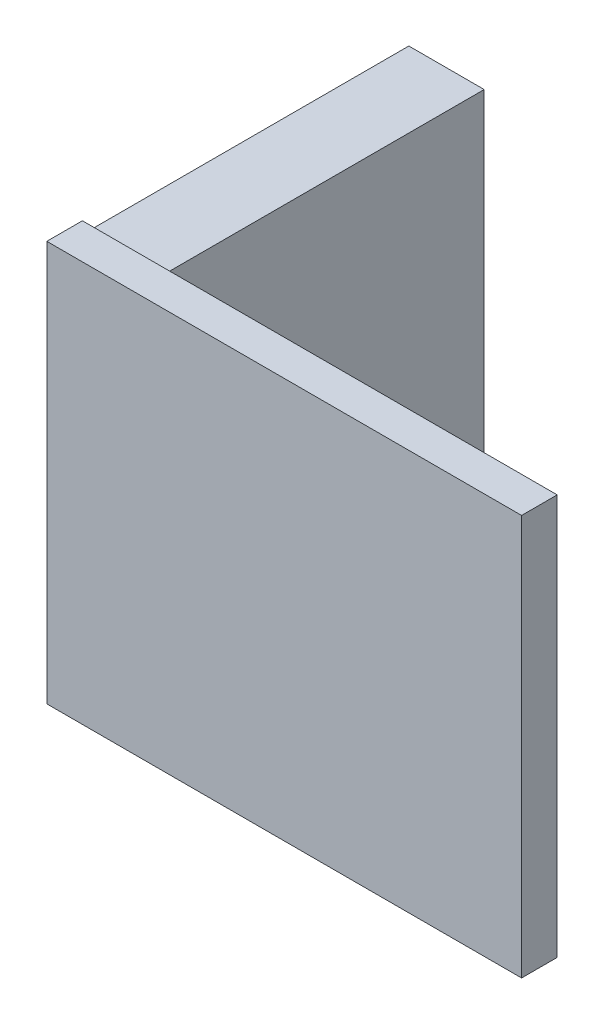
SolidWorks part; units mm, degrees
ref_plane "前视基准面" through (0, 0, 0) normal (0, 0, 1) x (1, 0, 0)
ref_plane "上视基准面" through (0, 0, 0) normal (0, 1, 0) x (1, 0, 0)
ref_plane "右视基准面" through (0, 0, 0) normal (1, 0, 0) x (0, 0, -1)
sketch "草图1" plane through (0, 0, 0) normal (0, 0, 1) x (1, 0, 0)
  line L1 (-63.8811, 39.7511) -> (-66.4211, 39.7511)
  line L2 (-63.8811, 39.7511) -> (-63.8811, 52.4511)
  line L3 (-63.8811, 52.4511) -> (-66.4211, 52.4511)
  line L4 (-66.4211, 39.7511) -> (-66.4211, 52.4511)
  point P4 (-63.8857, 39.8799)
  point P5 (0, 0)
  dimension "D1" = 2.54
  dimension "D2" = 12.7
extrude "凸台-拉伸1" add sketch "草图1" along normal blind 11
sketch "草图2" plane through (0, 0, 11) normal (0, 0, 1) x (1, 0, 0)
  line L1 (-66.4211, 52.8511) -> (-50.4211, 52.8511)
  line L2 (-66.4211, 52.8511) -> (-66.4211, 39.3511)
  line L3 (-66.4211, 39.3511) -> (-50.4211, 39.3511)
  line L4 (-50.4211, 52.8511) -> (-50.4211, 39.3511)
  line L5 (-66.4211, 52.4511) -> (-66.4211, 39.7511) construction
  line L6 (-63.8811, 52.4511) -> (-66.4211, 52.4511) construction
  line L7 (-66.4211, 39.7511) -> (-63.8811, 39.7511) construction
  point P6 (0, 0)
  dimension "D1" = 0.4
  dimension "D2" = 0.4
  dimension "D3" = 16
extrude "凸台-拉伸2" add sketch "草图2" along normal blind 1.2
